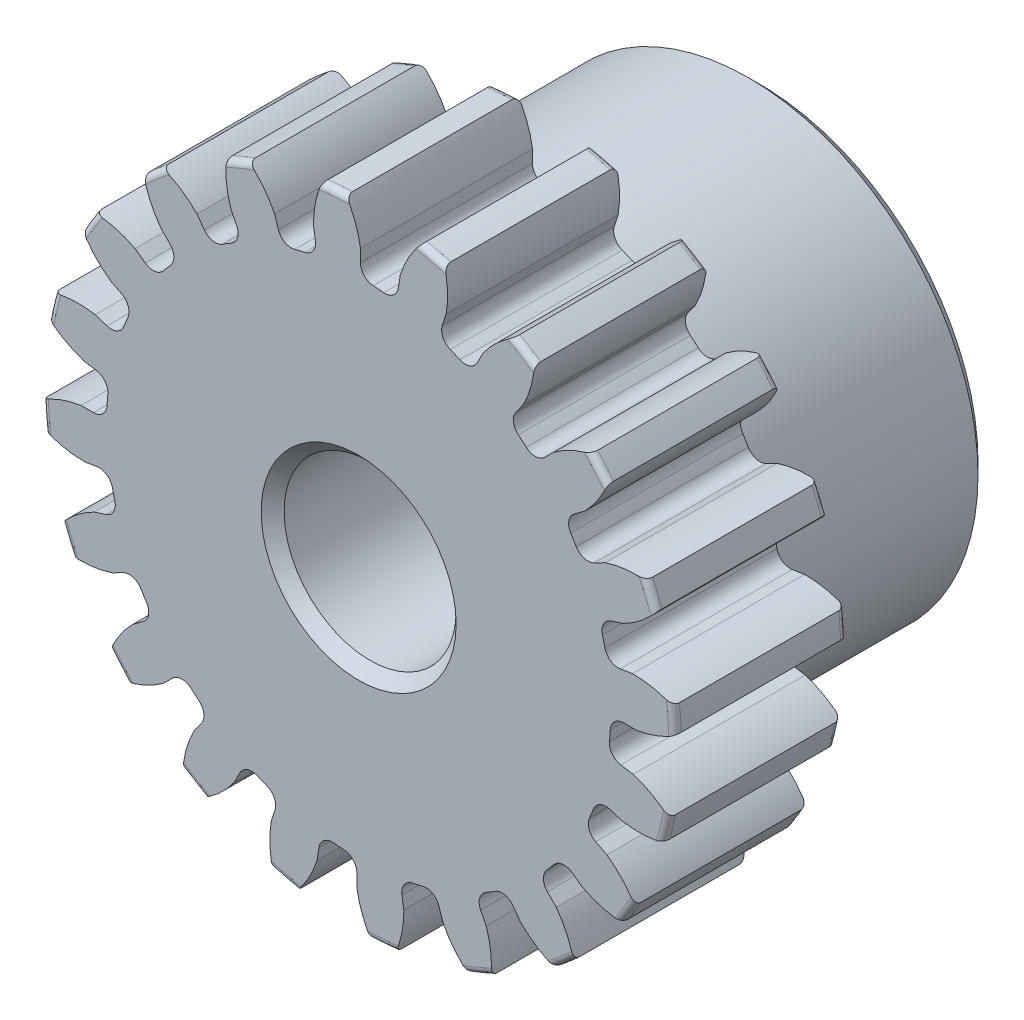
SolidWorks part; units mm, degrees
ref_plane "Front" through (0, 0, 0) normal (0, 0, 1) x (1, 0, 0)
ref_plane "Top" through (0, 0, 0) normal (0, 1, 0) x (1, 0, 0)
ref_plane "Right" through (0, 0, 0) normal (1, 0, 0) x (0, 0, -1)
sketch "Sketch1" plane through (0, 0, 0) normal (0, 0, 1) x (1, 0, 0)
  line L0 (-254, 0) -> (254, 0) construction
  circle A0 centre (0, 0) radius 8.763
  circle A1 centre (0, 0) radius 7.9375 construction
  circle A3 centre (0, 0) radius 6.9771 construction
  dimension "D1" = 1.7859
  dimension "OD" = 17.526
  dimension "Ptich Dia" = 15.875
  dimension "Root Dia" = 13.9541
  dimension "D3" = 0.8255
  dimension "Number of Teeth" = 508
extrude "Boss-Extrude1" add sketch "Sketch1" against normal blind 4.7625
sketch "Sketch2" plane through (0, 0, 0) normal (1, 0, 0) x (0, 0, -1)
  line L0 (4.7625, 0) -> (11.1125, 0)
  line L1 (4.7625, 0) -> (4.7625, 6.35)
  line L2 (4.7625, 6.35) -> (11.1125, 6.35)
  line L3 (11.1125, 6.35) -> (11.1125, 0)
  point P5 (11.1125, -6.35)
  point P6 (0, -8.763)
  point P7 (4.7625, -8.763)
  point P9 (0, 8.763)
  dimension "Face Wd" = 4.7625
  dimension "B Hub Dia" = 12.7
  dimension "D O'all Lg." = 11.1125
revolve "Revolve1" add sketch "Sketch2" angle 360 about L0
fillet "Fillet2" radius 0.1753 3 edges at (8.763, 0, -4.7625) (8.763, 0, 0) (6.35, 0, -4.7625)
sketch "Sketch3" plane through (0, 0, 0) normal (0, 0, 1) x (1, 0, 0)
  line L0 (0, 0) -> (0, 8.763) construction
  line L1 (-1.9241, 7.4399) -> (0, 7.9375)
  line L2 (-9.5921, 7.9375) -> (9.5921, 7.9375) construction
  line L3 (-9.2865, 5.5358) -> (9.2865, 10.3392) construction
  line L4 (-1.9241, 7.4399) -> (0, 0) construction
  line L5 (-4.9077, 5.9134) -> (0, 0) construction
  line L6 (-4.9077, 5.9134) -> (-0.7981, 9.3241) construction
  line L7 (-1.3417, 7.5666) -> (0, 0) construction
  line L8 (-1.3417, 7.5666) -> (0.0282, 7.8095) construction
  arc A0 (-1.9241, 7.4399) -> (-4.9077, 5.9134) centre (0, 0) ccw
  circle A1 centre (0, 0) radius 7.9375 construction
  circle A2 centre (0, 0) radius 7.6847 construction
  arc A3 (-1.9241, 7.4399) -> (-1.3417, 7.5666) centre (0, 0) cw
  circle A4 centre (0, 0) radius 8.763 construction
  point P6 (0, 7.9375)
  dimension "D1" = 1.9874
  dimension "Pressure Angle" = 14.5
  dimension "D2" = 3.3786
  dimension "D3" = 5.3406
  dimension "D4" = 0.5962
  dimension "D5" = 1.3912
sketch "Sketch4" plane through (0, 0, 0) normal (0, 0, 1) x (1, 0, 0)
  line L0 (0, 0) -> (0.6209, 7.8886) construction
  line L1 (0.0498, 7.6845) -> (0.0498, 6.9769)
  line L2 (0, 7.9375) -> (1.2417, 7.8398) construction
  line L3 (1.153, 7.5977) -> (1.0423, 6.8988)
  line L4 (0.0498, 6.9769) -> (0, 0) construction
  line L5 (0, 0) -> (0, 8.763) construction
  line L6 (-4.9077, 5.9134) -> (-0.7981, 9.3241) construction
  line L7 (-4.9077, 5.9134) -> (-0.7981, 9.3241) construction
  arc A0 (1.0423, 6.8988) -> (0.0498, 6.9769) centre (0, 0) ccw
  arc A1 (0, 7.9375) -> (1.2417, 7.8398) centre (0, 0) cw construction
  circle A2 centre (0, 0) radius 7.9375 construction
  circle A3 centre (0, 0) radius 7.6847 construction
  circle A4 centre (0, 0) radius 6.9771 construction
  arc A5 (2.2469, 9.0845) -> (-0.7981, 9.3241) centre (0, 0) ccw
  spline S0 degree 2 poles (-0.7981, 9.3241) (-0.0885, 8.6039) (0.0498, 7.6845) knots 0 0 0 1 1 1
  spline S1 degree 2 poles (2.2469, 9.0845) (1.4333, 8.4841) (1.153, 7.5977) knots 0 0 0 1 1 1
  dimension "D1" = 1.2468
extrude "Cut-Extrude1" cut sketch "Sketch4" against normal through all
fillet "Fillet1" radius 0.374 2 edges at (1.0423, 6.8988, -2.3813) (0.0498, 6.9769, -2.3813)
pattern_circular "CirPattern1" count 20 over 360 about axis through (0, 0, -4.7625) along (0, 0, 1) of "Cut-Extrude1", "Fillet1"
sketch "Sketch5" plane through (0, 0, 0) normal (0, 0, 1) x (1, 0, 0)
  circle A0 centre (0, 0) radius 2.3813
  circle A1 centre (0, 0) radius 1.5875 construction
  dimension "Bore Min" = 4.7625
  dimension "Bore Max" = 3.175
extrude "Cut-Extrude2" cut sketch "Sketch5" against normal through all
chamfer "Chamfer1" distance 0.3175 angle 45 3 edges at (6.35, 0, -11.1125) (2.3813, 0, 0) (2.3813, 0, -11.1125)
sketch "Pitch Dia" plane through (0, 0, 0) normal (0, 0, 1) x (1, 0, 0)
  circle A0 centre (0, 0) radius 7.9375 construction
  circle A1 centre (0, 0) radius 7.9375 construction
equation "\"D1@Boss-Extrude1\" = \"Face Wd@Sketch2\""
equation "\"D2@Sketch3\" = \"D1@Sketch3\"*1.7"
equation "\"D3@Sketch3\" = \"D1@Sketch3\"+\"D2@Sketch3\"-.001"
equation "\"D4@Sketch3\" = \"D1@Sketch3\"*.3"
equation "\"D5@Sketch3\" = \"D1@Sketch3\"-\"D4@Sketch3\""
equation "\"D1@Sketch4\" = 1.5708/(\"Number of Teeth@Sketch1\"/\"Ptich Dia@Sketch1\")"
equation "\"D1@Chamfer1\" = \"B Hub Dia@Sketch2\"*.025"
equation "\"D1@CirPattern1\" = \"Number of Teeth@Sketch1\""
equation "\"D1@Fillet1\" = \"D1@Sketch4\"*.3"
equation "\"D1@Fillet2\" = \"OD@Sketch1\"*.01"
equation "\"D1@Sketch1\" = 2.250/(\"Number of Teeth@Sketch1\"/\"Ptich Dia@Sketch1\")"
